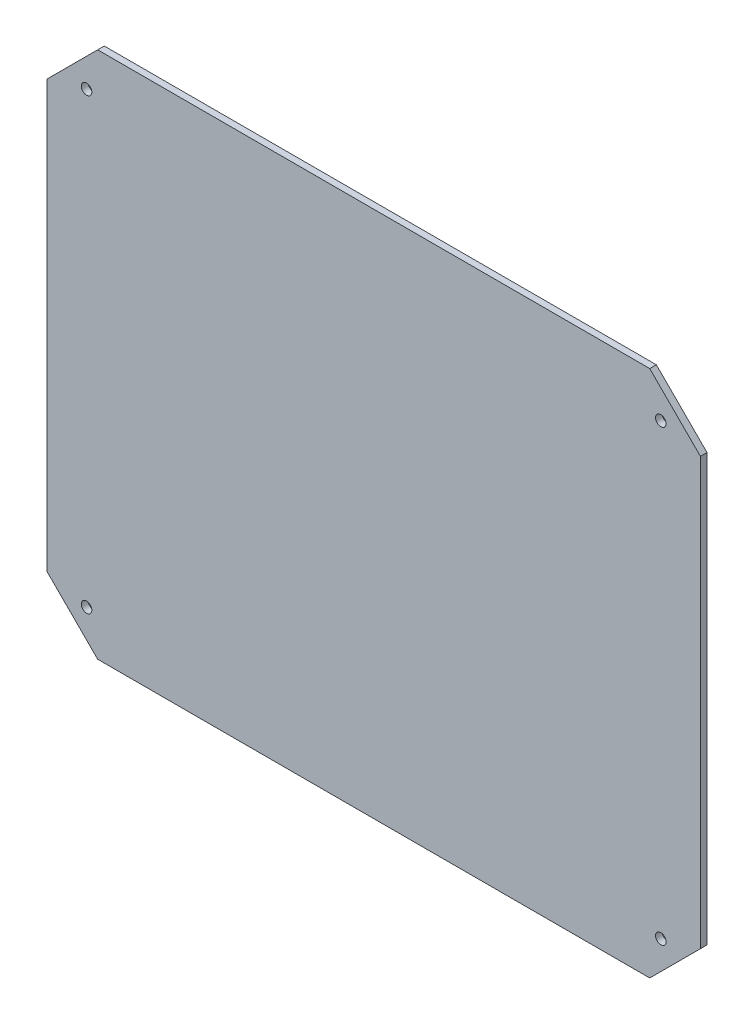
SolidWorks part; units mm, degrees
ref_plane "Plan de face" through (0, 0, 0) normal (0, 0, 1) x (1, 0, 0)
ref_plane "Plan de dessus" through (0, 0, 0) normal (0, 1, 0) x (1, 0, 0)
ref_plane "Plan de droite" through (0, 0, 0) normal (1, 0, 0) x (0, 0, -1)
sketch "Esquisse1" plane through (0, 0, 0) normal (0, 0, 1) x (1, 0, 0)
  line L0 (15.367, 0) -> (0, -15.367)
  line L1 (0, -15.367) -> (0, -144.653)
  line L2 (0, -144.653) -> (15.367, -160.02)
  line L3 (15.367, -160.02) -> (182.753, -160.02)
  line L4 (182.753, -160.02) -> (198.12, -144.653)
  line L5 (198.12, -144.653) -> (198.12, -15.367)
  line L6 (198.12, -15.367) -> (182.753, 0)
  line L7 (182.753, 0) -> (15.367, 0)
  line L8 (0, -80.01) -> (198.12, -80.01) construction
  line L9 (99.06, 0) -> (99.06, -160.02) construction
  circle A0 centre (12, -12) radius 1.6
  circle A1 centre (12, -148.02) radius 1.6
  circle A2 centre (186.12, -12) radius 1.6
  circle A3 centre (186.12, -148.02) radius 1.6
  dimension "D8" = 3.2
  dimension "D1" = 15.367
  dimension "D2" = 15.367
  dimension "D3" = 182.753
  dimension "D4" = 198.12
  dimension "D5" = 144.653
  dimension "D6" = 12
  dimension "D7" = 12
extrude "Boss.-Extru.1" add sketch "Esquisse1" along normal blind 2
